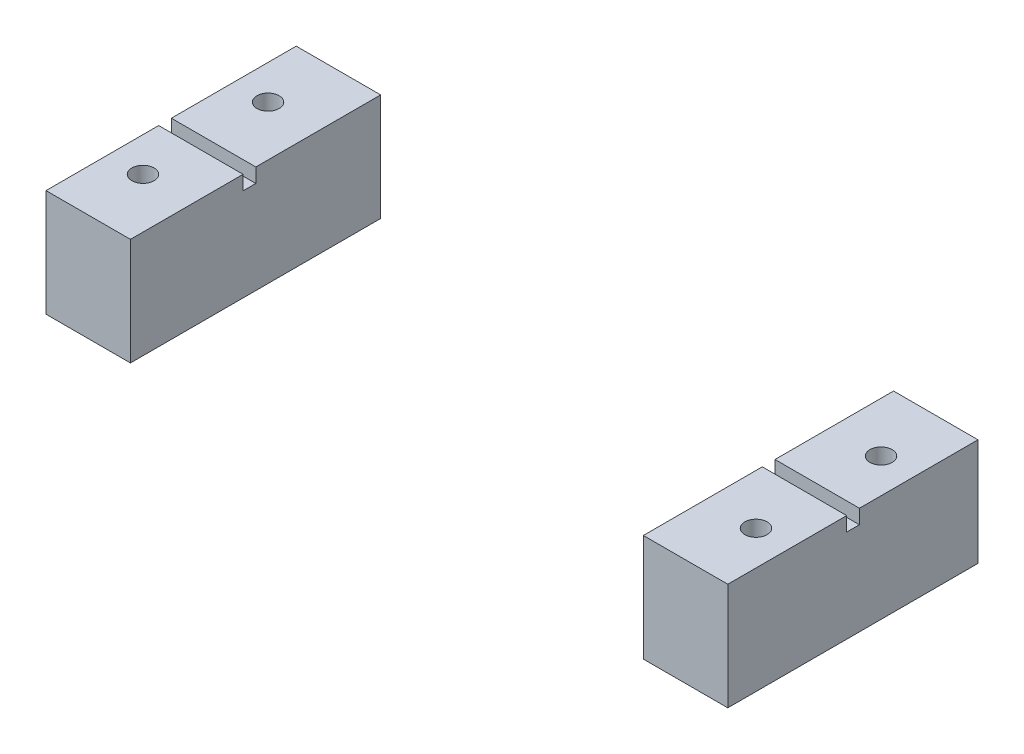
SolidWorks part; units mm, degrees
ref_plane "Front Plane" through (0, 0, 0) normal (0, 0, 1) x (1, 0, 0)
ref_plane "Top Plane" through (0, 0, 0) normal (0, 1, 0) x (1, 0, 0)
ref_plane "Right Plane" through (0, 0, 0) normal (1, 0, 0) x (0, 0, -1)
sketch "Sketch1" plane through (0, 0, 0) normal (0, 1, 0) x (1, 0, 0)
  line L0 (0, 20) -> (54.5, 0) construction
  line L1 (0, 0) -> (6.75, 0)
  line L2 (0, 0) -> (0, 20)
  line L3 (0, 20) -> (6.75, 20)
  line L4 (54.5, 0) -> (54.5, 20)
  line L5 (54.5, 20) -> (0, 0) construction
  line L6 (47.75, 20) -> (54.5, 20)
  line L7 (51.75, 5) -> (2.75, 5)
  line L8 (51.75, 5) -> (51.75, 15)
  line L9 (51.75, 15) -> (2.75, 15)
  line L10 (2.75, 5) -> (2.75, 15)
  line L11 (51.75, 5) -> (2.75, 15) construction
  line L12 (51.75, 15) -> (2.75, 5) construction
  line L13 (47.75, 0) -> (6.75, 0)
  line L14 (47.75, 0) -> (47.75, 20)
  line L15 (47.75, 0) -> (54.5, 0)
  line L16 (6.75, 0) -> (6.75, 20)
  line L17 (47.75, 0) -> (6.75, 20) construction
  line L18 (47.75, 20) -> (6.75, 0) construction
  circle A0 centre (2.75, 15) radius 0.889
  circle A1 centre (51.75, 15) radius 0.889
  circle A2 centre (51.75, 5) radius 0.889
  circle A3 centre (2.75, 5) radius 0.889
  point P5 (27.25, 10)
  point P10 (27.25, 10)
  dimension "D6" = 1.778
  dimension "D1" = 54.5
  dimension "D2" = 20
  dimension "D3" = 10
  dimension "D4" = 49
  dimension "D5" = 41
  dimension "D7" = 2
  dimension "D8" = 2
extrude "Boss-Extrude1" add sketch "Sketch1" along normal blind 8.5598 contours L7 L16 L9 L10 | L1 L16 L7 L10 L9 L3 L2 | L14 L7 L8 L9 | L14 L15 L4 L6 L9 L8 L7
sketch "Sketch2" plane through (0, 8.5598, 0) normal (0, 1, 0) x (1, 0, 0)
  line L0 (0, 0) -> (0, 20) construction
  line L1 (6.75, 10.0215) -> (0, 10.0215)
  line L2 (6.75, 10.0215) -> (6.75, 9.0055)
  line L3 (6.75, 9.0055) -> (0, 9.0055)
  line L4 (0, 10.0215) -> (0, 9.0055)
  line L5 (6.75, 10.0215) -> (0, 9.0055) construction
  line L6 (6.75, 9.0055) -> (0, 10.0215) construction
  line L7 (47.75, 0) -> (47.75, 20) construction
  line L8 (54.5, 10.5215) -> (47.75, 10.5215)
  line L9 (54.5, 10.5215) -> (54.5, 9.5055)
  line L10 (54.5, 9.5055) -> (47.75, 9.5055)
  line L11 (47.75, 10.5215) -> (47.75, 9.5055)
  line L12 (54.5, 10.5215) -> (47.75, 9.5055) construction
  line L13 (54.5, 9.5055) -> (47.75, 10.5215) construction
  point P0 (3.375, 9.5135)
  point P7 (51.125, 10.0135)
  dimension "D1" = 1.016
  dimension "D2" = 1.016
extrude "Cut-Extrude1" cut sketch "Sketch2" against normal blind 1.143
